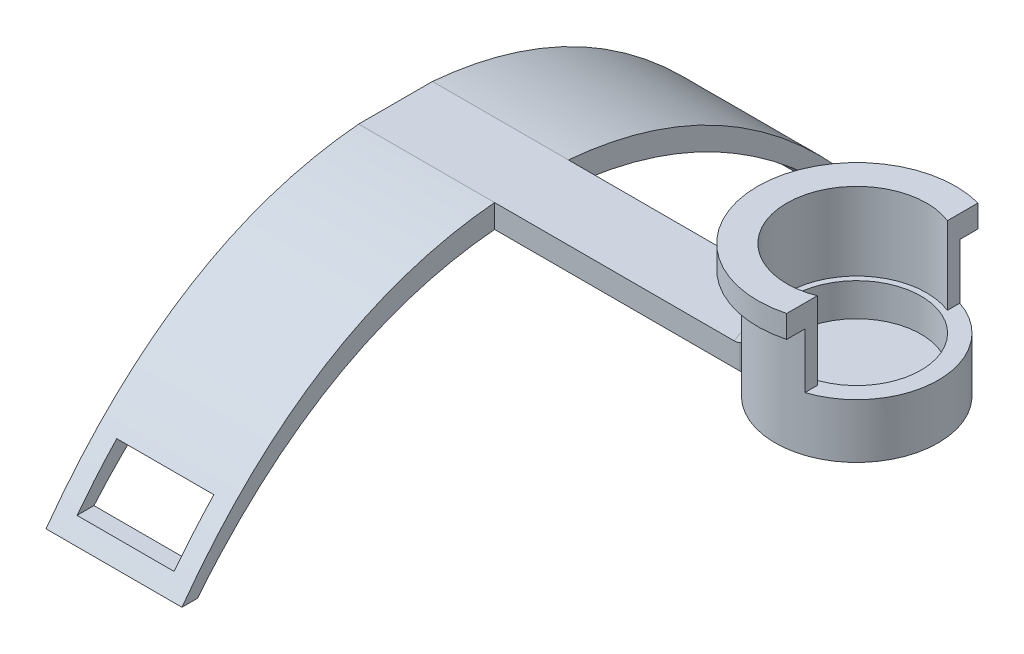
SolidWorks part; units mm, degrees
ref_plane "Front Plane" through (0, 0, 0) normal (0, 0, 1) x (1, 0, 0)
ref_plane "Top Plane" through (0, 0, 0) normal (0, 1, 0) x (1, 0, 0)
ref_plane "Right Plane" through (0, 0, 0) normal (1, 0, 0) x (0, 0, -1)
sketch "0.1mm fit for pot" plane through (0, 0, 0) normal (0, 1, 0) x (1, 0, 0)
  circle A1 centre (0, 0) radius 10.5
  dimension "D2" = 21
extrude "Boss-Extrude1" add sketch "0.1mm fit for pot" along normal blind 2.75
sketch "Sketch4" plane through (0, 2.75, 0) normal (0, 1, 0) x (1, 0, 0)
  circle A0 centre (0, 0) radius 8.275
  circle A1 centre (0, 0) radius 10.5 construction
  circle A2 centre (0, 0) radius 10.5
  dimension "D1" = 16.55
extrude "Boss-Extrude2" add sketch "Sketch4" along normal blind 4.25
sketch "Sketch5" plane through (0, 2.75, 0) normal (0, 1, 0) x (1, 0, 0)
  line L6 (-1, -8.2144) -> (-1, -7.0658)
  line L7 (-1, -7.0658) -> (0.9881, -7.0658)
  line L8 (0.9881, -7.0658) -> (0.9881, -8.2158)
  circle A0 centre (0, 0) radius 8.275 construction
  arc A1 (-1, -8.2144) -> (0.9881, -8.2158) centre (0, 0) ccw
  point P3 (0, -8.25)
  point P6 (0, -8.25)
  point P7 (0, -8.25)
  dimension "D1" = 1.15
extrude "Boss-Extrude3" add sketch "Sketch5" along normal blind 2
fillet "Fillet1" radius 0.25 5 edges at (-1, 4.75, 7.6401) (0.9881, 4.75, 7.6408) (0.9881, 3.75, 7.0658) (-0.006, 4.75, 7.0658) (-1, 3.75, 7.0658)
sketch "Sketch7" plane through (0, 7, 0) normal (0, 1, 0) x (1, 0, 0)
  line L0 (3.2996, 9.9681) -> (3.2996, 8.3733)
  line L1 (3.2996, -8.3733) -> (3.2996, -9.9681)
  arc A0 (3.2996, 9.9681) -> (3.2996, -9.9681) centre (0, 0) ccw
  arc A1 (3.2996, 8.3733) -> (3.2996, -8.3733) centre (0, 0) ccw
  dimension "D1" = 18
  dimension "D2" = 21
extrude "Boss-Extrude6" add sketch "Sketch7" along normal blind 10
sketch "Sketch8" plane through (0, 17, 0) normal (0, 1, 0) x (1, 0, 0)
  line L0 (3.2996, 12.3156) -> (3.2996, 9.9681)
  line L1 (3.2996, -9.9681) -> (3.2996, -12.3156)
  arc A0 (3.2996, 12.3156) -> (3.2996, -12.3156) centre (0, 0) ccw
  arc A1 (3.2996, 9.9681) -> (3.2996, -9.9681) centre (0, 0) ccw construction
  arc A2 (3.2996, 9.9681) -> (3.2996, -9.9681) centre (0, 0) ccw
  dimension "D1" = 2.25
extrude "Boss-Extrude7" add sketch "Sketch8" against normal blind 2.9
sketch "Sketch9" plane through (0, 0, 0) normal (0, -1, 0) x (1, 0, 0)
  line L3 (-9.3642, 4.75) -> (-59.3642, 4.75)
  line L5 (-9.3642, -4.75) -> (-59.3642, -4.75)
  line L6 (-59.3642, 4.75) -> (-59.3642, -4.75)
  circle A0 centre (0, 0) radius 10.5 construction
  arc A1 (-9.3642, 4.75) -> (-9.3642, -4.75) centre (0, 0) ccw
  point P10 (-5.25, 0)
  dimension "D1" = 50
extrude "Boss-Extrude8" add sketch "Sketch9" against normal blind 3
fillet "Fillet2" radius 1.5 3 edges at (-9.3642, 1.5, -4.75) (-9.3642, 1.5, 4.75) (-10.5, 3, 0)
sketch "Sketch10" plane through (-59.3642, 0, 0) normal (-1, 0, 0) x (0, 0, 1)
  line L0 (0, 3) -> (0, -22) construction
  line L1 (4.75, 3) -> (-4.75, 3) construction
  line L2 (45, -22) -> (-45, -22) construction
  line L3 (-45, -22) -> (-43, -22)
  line L4 (45, -22) -> (43, -22)
  line L5 (-4.75, 3) -> (4.75, 3)
  line L6 (4.75, 0) -> (-4.75, 0)
  spline S0 degree 2 poles (-45, -22) (-28.3868, 0.9123) (-4.75, 3) knots 0 0 0 0.454443 0.454443 0.454443
  spline S1 degree 2 poles (43, -22) (26.7622, -1.9487) (4.75, 0) knots 0 0 0 0.451407 0.451407 0.451407
  spline S2 degree 2 poles (4.75, 3) (28.3868, 0.9123) (45, -22) knots 0.545557 0.545557 0.545557 1 1 1
  spline S3 degree 2 poles (-4.75, 0) (-26.7622, -1.9487) (-43, -22) knots 0.548593 0.548593 0.548593 1 1 1
  point P8 (0, -22)
  dimension "D1" = 25
  dimension "D2" = 90
  dimension "D3" = 2
  dimension "D4" = 2
extrude "Boss-Extrude9" add sketch "Sketch10" against normal blind 17.5
sketch "Sketch11" plane through (0, 0, -4.75) normal (0, 0, -1) x (-1, 0, 0)
  line L0 (50.6142, -22) -> (50.6142, -20) construction
  line L1 (41.8642, -22) -> (59.3642, -22) construction
  line L2 (56.8642, -20) -> (44.3642, -20) construction
  line L4 (44.3642, -20) -> (56.8642, -20)
  line L5 (44.3642, -20) -> (44.3642, -14)
  line L6 (44.3642, -14) -> (56.8642, -14)
  line L7 (56.8642, -20) -> (56.8642, -14)
  point P7 (50.6142, -20)
  dimension "D1" = 12.5
  dimension "D2" = 6
  dimension "D3" = 2
extrude "Cut-Extrude1" cut sketch "Sketch11" against normal through all both and the other way through all
